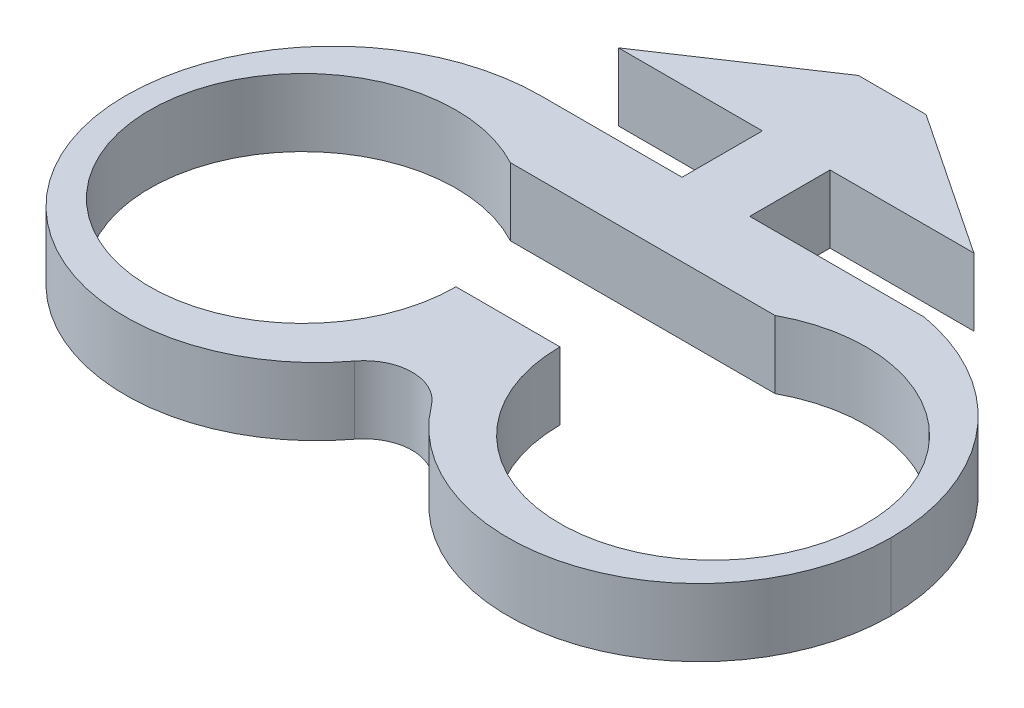
SolidWorks part; units mm, degrees
ref_plane "Front" through (0, 0, 0) normal (0, 0, 1) x (1, 0, 0)
ref_plane "Top" through (0, 0, 0) normal (0, 1, 0) x (1, 0, 0)
ref_plane "Right" through (0, 0, 0) normal (1, 0, 0) x (0, 0, -1)
sketch "Sketch1" plane through (0, 0, 0) normal (0, 1, 0) x (1, 0, 0)
  line L0 (-1.7907, 2.125) -> (-9.398, 2.125)
  line L2 (-1.7907, -2.125) -> (-1.7907, 2.125)
  line L4 (1.7907, -2.125) -> (1.7907, 2.125)
  line L7 (-9.398, 2.125) -> (-1.7907, 7.205)
  line L8 (-1.7907, 7.205) -> (1.7907, 7.205)
  line L9 (1.7907, 7.205) -> (9.398, 2.125)
  line L10 (9.398, 2.125) -> (1.7907, 2.125)
  line L11 (1.7907, -2.125) -> (20.25, -2.125)
  line L12 (-1.7907, -2.125) -> (-20.25, -2.125)
  line L13 (-20.25, -2.125) -> (-20.25, -13.1232)
  line L14 (-20.25, -13.1232) -> (20.25, -13.1232)
  line L15 (20.25, -13.1232) -> (20.25, -2.125)
  line L16 (20.25, -2.125) -> (1.7907, -2.125)
  point P0 (0, 0)
  point P17 (0, 7.205)
  point P19 (0, -13.1232)
  point P24 (1.7907, 0)
  dimension "D1" = 18.796
  dimension "D2" = 3.5814
  dimension "D3" = 40.5
  dimension "D4" = 10.9982
  dimension "D5" = 5.08
  dimension "4.2" = 4.25
extrude "Boss-Extrude1" add sketch "Sketch1" along normal blind 3.5814 contours L14 L15 L11 L4 L10 L9 L8 L7 L0 L2 L12 L13
sketch "Sketch3" plane through (0, 3.5814, 0) normal (0, 1, 0) x (1, 0, 0)
  line L3 (-20.25, -13.1232) -> (20.25, -13.1232) construction
  line L16 (-20.25, -13.1232) -> (20.25, -13.1232)
  line L17 (20.25, -13.1232) -> (20.25, -2.125)
  line L18 (20.25, -2.125) -> (1.7907, -2.125)
  line L19 (1.7907, -2.125) -> (1.7907, 2.125)
  line L20 (1.7907, 2.125) -> (9.398, 2.125)
  line L21 (9.398, 2.125) -> (1.7907, 7.205)
  line L22 (1.7907, 7.205) -> (-1.7907, 7.205)
  line L23 (-1.7907, 7.205) -> (-9.398, 2.125)
  line L24 (-9.398, 2.125) -> (-1.7907, 2.125)
  line L25 (-1.7907, 2.125) -> (-1.7907, -2.125)
  line L26 (-1.7907, -2.125) -> (-20.25, -2.125)
  line L27 (-20.25, -2.125) -> (-20.25, -13.1232)
  line L28 (-20.25, -13.1232) -> (20.25, -13.1232)
  arc A2 (-20.25, -13.1232) -> (-2.0306, -19.2057) centre (-10.125, -13.1232) ccw
  arc A3 (2.0306, -19.2057) -> (20.25, -13.1232) centre (10.125, -13.1232) ccw
  arc A4 (2.0306, -19.2057) -> (-2.0306, -19.2057) centre (0, -20.7315) ccw
  point P14 (0, -13.1232)
  line M15 (-20.25, -13.1232) -> (20.25, -13.1232)
  dimension "D2" = 2.54
  dimension "D1" = 0
extrude "Boss-Extrude2" add sketch "Sketch3" against normal up to surface (3.5814 mm away) contours A2 M15 | L28 A3 up to face at (0, 0, 0.9864)
sketch "Sketch4" plane through (0, 3.5814, 0) normal (0, 1, 0) x (1, 0, 0)
  line L1 (2.75, -13.1232) -> (-2.75, -13.1232) construction
  circle A0 centre (-10.85, -13.1232) radius 8.1
  circle A1 centre (10.85, -13.1232) radius 8.1
  point P4 (0, -13.1232)
  dimension "D1" = 16.2
  dimension "D2" = 21.7
extrude "Cut-Extrude2" cut sketch "Sketch4" against normal through all
sketch "Sketch5" plane through (0, 3.5814, 0) normal (0, 1, 0) x (1, 0, 0)
  line L2 (7, -5.9967) -> (-7, -5.9967)
  line L10 (-2.75, -13.1232) -> (2.75, -13.1232)
  circle A0 centre (-10.85, -13.1232) radius 8.1 construction
  circle A1 centre (10.85, -13.1232) radius 8.1 construction
  arc A8 (7, -5.9967) -> (2.75, -13.1232) centre (10.85, -13.1232) ccw
  arc A9 (-2.75, -13.1232) -> (-7, -5.9967) centre (-10.85, -13.1232) ccw
  point P12 (0, -15.6632)
  point P28 (0, -10.5832)
  dimension "D2" = 14
  dimension "D3" = 2.54
  dimension "D10" = 2.54
extrude "Cut-Extrude4" cut sketch "Sketch5" against normal up to next contours A9 L2 A8 L10
sketch "Sketch6" plane through (0, 3.5814, 0) normal (0, 1, 0) x (1, 0, 0)
  line L0 (-9.2518, -2.125) -> (-20.25, -2.125)
  line L1 (-20.25, -2.125) -> (-20.25, -13.1232)
  line L2 (-1.7907, -2.125) -> (-20.25, -2.125) construction
  line L3 (20.25, -13.1232) -> (20.25, -2.125)
  line L4 (20.25, -2.125) -> (11.0204, -2.125)
  line L5 (1.7907, -2.125) -> (20.25, -2.125) construction
  arc A0 (-9.2518, -2.125) -> (-20.25, -13.1232) centre (-9.2518, -13.1232) ccw
  arc A2 (20.25, -13.1232) -> (11.0204, -2.125) centre (9.0824, -13.1232) ccw
extrude "Cut-Extrude5" cut sketch "Sketch6" against normal up to next
